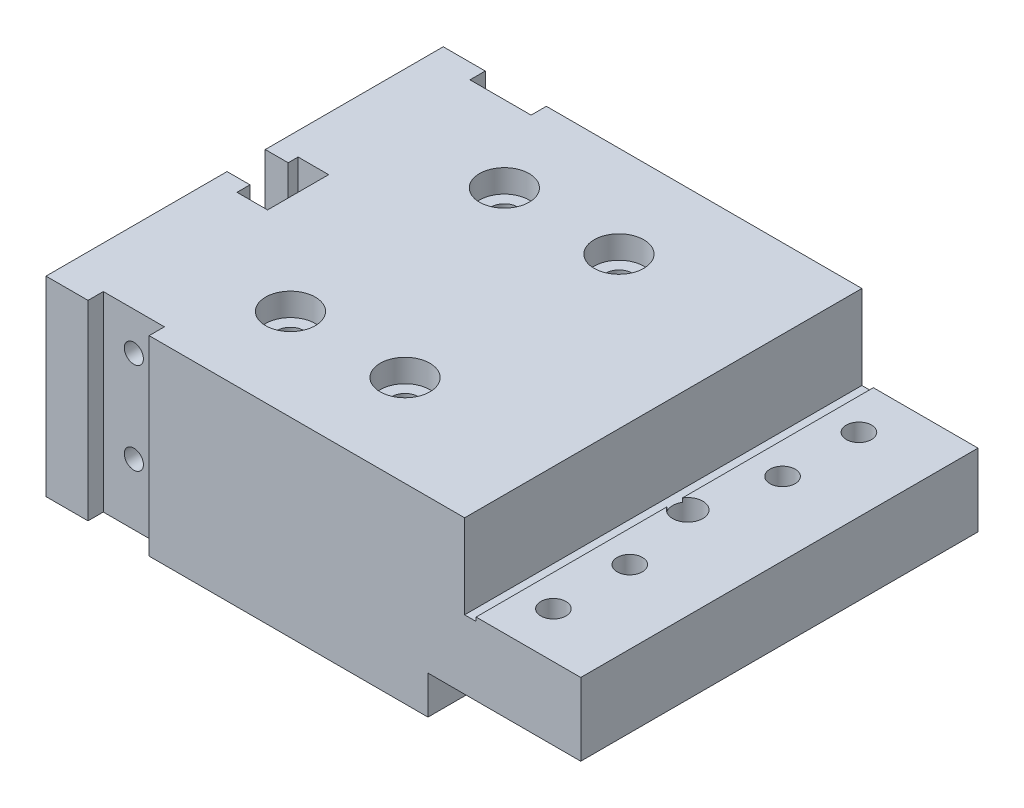
SolidWorks part; units mm, degrees
ref_plane "Front Plane" through (0, 0, 0) normal (0, 0, 1) x (1, 0, 0)
ref_plane "Top Plane" through (0, 0, 0) normal (0, 1, 0) x (1, 0, 0)
ref_plane "Right Plane" through (0, 0, 0) normal (1, 0, 0) x (0, 0, -1)
sketch "Sketch1" plane through (0, 0, 0) normal (0, 0, 1) x (1, 0, 0)
  line L1 (-25.8157, -13.5065) -> (28.9843, -13.5065)
  line L2 (-25.8157, -13.5065) -> (-25.8157, -38.5065)
  line L3 (-25.8157, -38.5065) -> (24.1843, -38.5065)
  line L4 (28.9843, -13.5065) -> (28.9843, -24.5065)
  line L8 (24.1843, -38.5065) -> (24.1843, -33.5065)
  line L9 (28.9843, -24.5065) -> (30.4843, -24.5065)
  line L10 (30.4843, -24.0065) -> (30.4843, -24.5065)
  line L11 (30.4843, -24.0065) -> (44.1843, -24.0065)
  line L13 (24.1843, -33.5065) -> (44.1843, -33.5065)
  line L14 (44.1843, -24.0065) -> (44.1843, -33.5065)
  dimension "D1" = 54.8
  dimension "D2" = 25
  dimension "D3" = 5
  dimension "D4" = 14.5
  dimension "D5" = 0.5
  dimension "D6" = 1.5
  dimension "D7" = 50
  dimension "D8" = 20
extrude "Boss-Extrude1" add sketch "Sketch1" along normal blind 52
sketch "Sketch2" plane through (0, -13.5065, 0) normal (0, 1, 0) x (1, 0, 0)
  line L0 (28.9843, -52) -> (-25.8157, -52) construction
  line L1 (-12.3157, -52) -> (-20.3157, -52)
  line L2 (-12.3157, -52) -> (-12.3157, -50)
  line L3 (-12.3157, -50) -> (-20.3157, -50)
  line L4 (-20.3157, -52) -> (-20.3157, -50)
  line L5 (28.9843, 0) -> (-25.8157, 0) construction
  line L6 (-20.3157, 0) -> (-12.3157, 0)
  line L7 (-20.3157, 0) -> (-20.3157, -2)
  line L8 (-20.3157, -2) -> (-12.3157, -2)
  line L9 (-12.3157, 0) -> (-12.3157, -2)
  line L10 (-25.8157, -52) -> (-25.8157, 0) construction
  line L11 (-22.8157, -23.3) -> (-25.8157, -23.3)
  line L12 (-25.8157, -23.3) -> (-25.8157, -28.3)
  line L13 (-25.8157, -28.3) -> (-22.8157, -28.3)
  line L15 (-22.8157, -28.3) -> (-22.8157, -30)
  line L16 (-22.8157, -22) -> (-18.8157, -22)
  line L17 (-22.8157, -22) -> (-22.8157, -23.3)
  line L18 (-22.8157, -30) -> (-18.8157, -30)
  line L19 (-18.8157, -22) -> (-18.8157, -30)
  circle A0 centre (-5.8157, -12) radius 1.7
  circle A1 centre (9.1843, -12) radius 1.7
  circle A2 centre (-5.8157, -40) radius 1.7
  circle A3 centre (9.1843, -40) radius 1.7
  point P30 (-16.3157, -50)
  dimension "D5" = 3.4
  dimension "D1" = 9.5
  dimension "D2" = 8
  dimension "D3" = 2
  dimension "D4" = 2
  dimension "D6" = 20
  dimension "D7" = 35
  dimension "D8" = 12
  dimension "D9" = 40
  dimension "D10" = 23.7
  dimension "D11" = 28.7
  dimension "D12" = 30
  dimension "D13" = 22
  dimension "D14" = 3
  dimension "D15" = 4
extrude "Cut-Extrude1" cut sketch "Sketch2" against normal blind 52
sketch "Sketch3" plane through (0, -13.5065, 0) normal (0, 1, 0) x (1, 0, 0)
  circle A0 centre (-5.8157, -12) radius 3.25
  circle A1 centre (9.1843, -12) radius 3.25
  circle A2 centre (9.1843, -40) radius 3.25
  circle A3 centre (-5.8157, -40) radius 3.25
  dimension "D1" = 6.5
extrude "Cut-Extrude2" cut sketch "Sketch3" against normal blind 3
sketch "Sketch4" plane through (0, -24.0065, 0) normal (0, 1, 0) x (1, 0, 0)
  line L0 (44.1843, -52) -> (30.4843, -52) construction
  line L1 (-25.8157, -52) -> (-25.8157, -28.3) construction
  circle A0 centre (32.1843, -26) radius 1.9781
  dimension "D1" = 26
  dimension "D2" = 58
extrude "Cut-Extrude3" cut sketch "Sketch4" against normal through all
hole_wizard "M4 Tapped Hole1" positions "Sketch5" profile "Sketch6" tap size "M4" standard "ISO"
sketch "Sketch5" plane through (0, -24.0065, 0) normal (0, 1, 0) x (1, 0, 0)
  line L0 (44.1843, -52) -> (30.4843, -52) construction
  point P0 (34.6007, -6)
  point P2 (34.6007, -16)
  point P4 (34.6007, -36)
  point P6 (34.6007, -46)
  dimension "D1" = 6
  dimension "D2" = 16
  dimension "D3" = 36
  dimension "D4" = 46
sketch "Sketch6" plane through (34.6007, -24.0065, 6) normal (1, 0, 0) x (0, 0, 1)
  line L0 (0, 0) -> (0, 11.0914)
  line L1 (0, 11.0914) -> (1.65, 10.1)
  line L2 (1.65, 10.1) -> (1.65, 0)
  line L5 (1.65, 0) -> (0, 0)
  line L10 (0, 11.0914) -> (-1.65, 10.1) construction
  line L11 (0, -6.35) -> (0, 107.95) construction
  dimension "Tap Drill Dia." = 3.3
  dimension "Tap Drill Depth" = 10.1
  dimension "Drill Angle" = 118
cosmetic thread "Hole Thread1" parameters "D1"=8, "D2"=4
cosmetic thread "Hole Thread2" parameters "D1"=8, "D2"=4
cosmetic thread "Hole Thread3" parameters "D1"=8, "D2"=4
cosmetic thread "Hole Thread4" parameters "D1"=8, "D2"=4
sketch "Sketch7" plane through (24.1843, 0, 0) normal (1, 0, 0) x (0, 0, -1)
  line L0 (-52, -38.5065) -> (0, -38.5065) construction
  line L1 (-46, -38.5065) -> (-6, -38.5065)
  line L2 (-46, -38.5065) -> (-46, -35.5065)
  line L3 (-46, -35.5065) -> (-6, -35.5065)
  line L4 (-6, -38.5065) -> (-6, -35.5065)
  line L5 (-52, -38.5065) -> (-52, -33.5065) construction
  dimension "D1" = 6
  dimension "D2" = 40
  dimension "D3" = 3
extrude "Cut-Extrude4" cut sketch "Sketch7" against normal through all
hole_wizard "M3 Tapped Hole1" positions "Sketch8" profile "Sketch9" tap size "M3" standard "ISO"
sketch "Sketch8" plane through (0, 0, 50) normal (0, 0, 1) x (1, 0, 0)
  line L0 (-25.8157, -13.5065) -> (-25.8157, -38.5065) construction
  line L1 (-12.3157, -38.5065) -> (-20.3157, -38.5065) construction
  point P0 (-16.3157, -18.5065)
  point P2 (-16.3157, -30.5065)
  dimension "D1" = 9.5
  dimension "D2" = 8
  dimension "D3" = 9.5
  dimension "D4" = 20
sketch "Sketch9" plane through (-16.3157, -18.5065, 50) normal (1, 0, 0) x (0, -1, 0)
  line L0 (0, 0) -> (0, 8.2511)
  line L1 (0, 8.2511) -> (1.25, 7.5)
  line L2 (1.25, 7.5) -> (1.25, 0)
  line L5 (1.25, 0) -> (0, 0)
  line L10 (0, 8.2511) -> (-1.25, 7.5) construction
  line L11 (0, -6.35) -> (0, 107.95) construction
  dimension "Tap Drill Dia." = 2.5
  dimension "Tap Drill Depth" = 7.5
  dimension "Drill Angle" = 118
cosmetic thread "Hole Thread5" parameters "D1"=6, "D2"=3
cosmetic thread "Hole Thread6" parameters "D1"=6, "D2"=3
hole_wizard "M3 Tapped Hole2" positions "Sketch10" profile "Sketch11" tap size "M3" standard "ISO"
sketch "Sketch10" plane through (0, 0, 2) normal (0, 0, -1) x (-1, 0, 0)
  line L0 (25.8157, -13.5065) -> (25.8157, -38.5065) construction
  line L1 (20.3157, -38.5065) -> (12.3157, -38.5065) construction
  point P0 (16.3157, -18.5065)
  point P2 (16.3157, -30.5065)
  dimension "D1" = 9.5
  dimension "D2" = 9.5
  dimension "D3" = 8
  dimension "D4" = 20
sketch "Sketch11" plane through (-16.3157, -18.5065, 2) normal (1, 0, 0) x (0, 1, 0)
  line L0 (0, 0) -> (0, 8.2511)
  line L1 (0, 8.2511) -> (1.25, 7.5)
  line L2 (1.25, 7.5) -> (1.25, 0)
  line L5 (1.25, 0) -> (0, 0)
  line L10 (0, 8.2511) -> (-1.25, 7.5) construction
  line L11 (0, -6.35) -> (0, 107.95) construction
  dimension "Tap Drill Dia." = 2.5
  dimension "Tap Drill Depth" = 7.5
  dimension "Drill Angle" = 118
cosmetic thread "Hole Thread7" parameters "D1"=6, "D2"=3
cosmetic thread "Hole Thread8" parameters "D1"=6, "D2"=3
